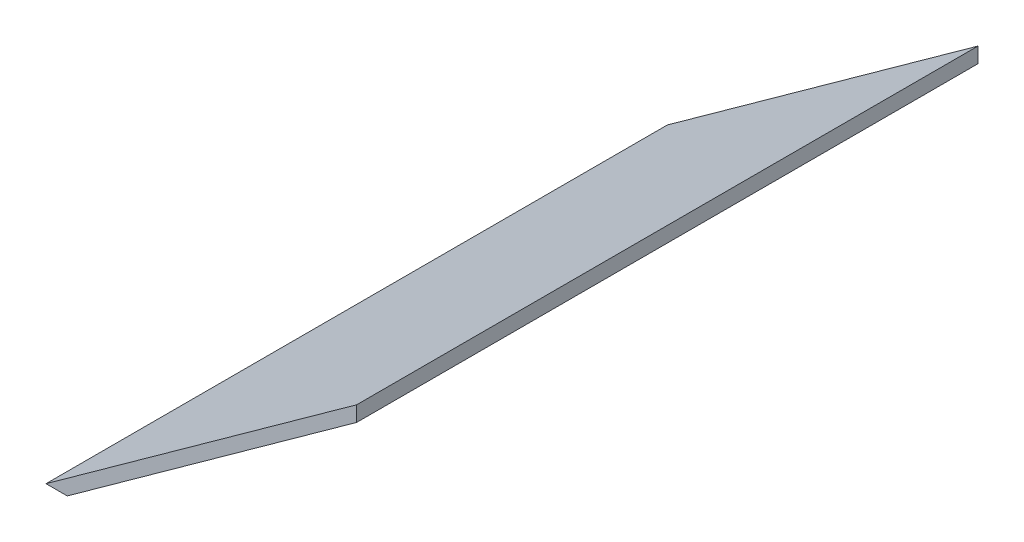
SolidWorks part; units mm, degrees
ref_plane "Ön Düzlem" through (0, 0, 0) normal (0, 0, 1) x (1, 0, 0)
ref_plane "Üst Düzlem" through (0, 0, 0) normal (0, 1, 0) x (1, 0, 0)
ref_plane "Sağ Düzlem" through (0, 0, 0) normal (1, 0, 0) x (0, 0, -1)
sketch "Sketch2" plane through (0, 0, 0) normal (0, 0, 1) x (1, 0, 0)
  line L0 (-125, 0) -> (125, 180)
  line L1 (0, 90) -> (5.843, 81.8847) construction
  line L2 (5.843, 81.8847) -> (-107.8856, 0)
  line L3 (-107.8856, 0) -> (-125, 0)
  line L4 (5.843, 81.8847) -> (125, 167.6777)
  line L5 (125, 167.6777) -> (125, 180)
  point P2 (0, 90)
  dimension "D1" = 250
  dimension "D2" = 180
  dimension "D3" = 10
extrude "Boss-Extrude1" add sketch "Sketch2" along normal blind 500
